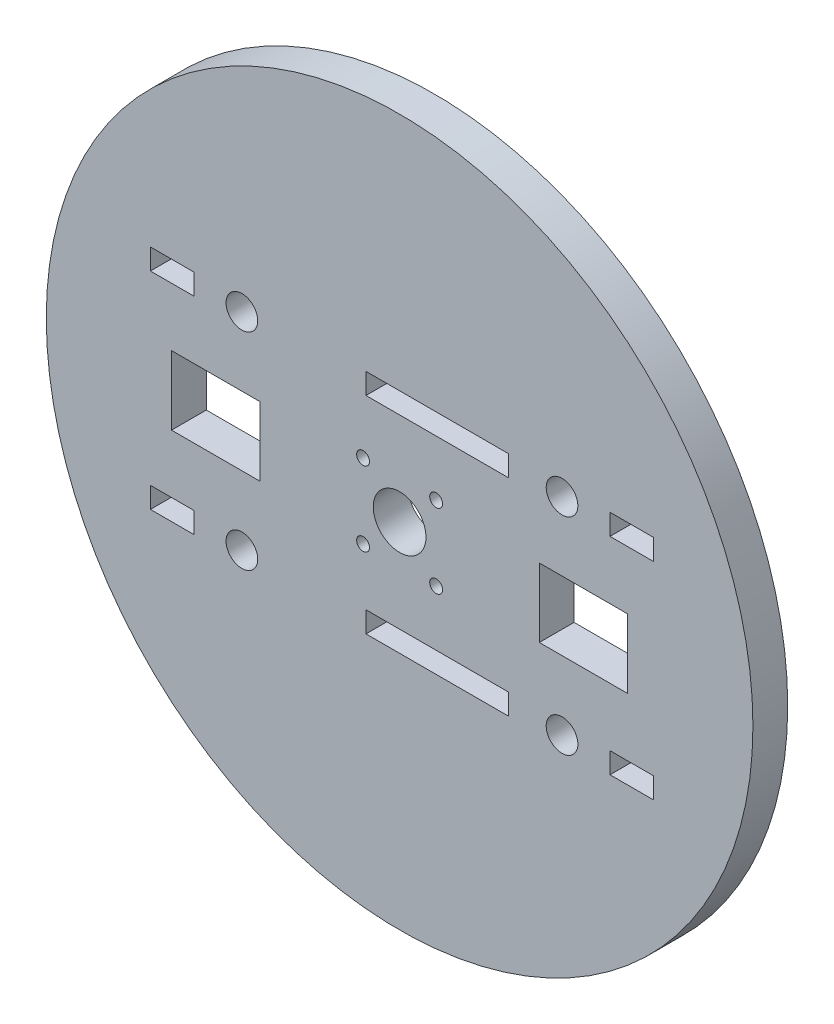
SolidWorks part; units mm, degrees
ref_plane "Front Plane" through (0, 0, 0) normal (0, 0, 1) x (1, 0, 0)
ref_plane "Top Plane" through (0, 0, 0) normal (0, 1, 0) x (1, 0, 0)
ref_plane "Right Plane" through (0, 0, 0) normal (1, 0, 0) x (0, 0, -1)
sketch "Sketch3" plane through (0, 0, 0) normal (0, 0, 1) x (1, 0, 0)
  line L4 (27.9395, 102.4605) -> (40.6396, 102.4605)
  line L5 (27.9395, 102.4605) -> (27.9395, 112.3605)
  line L6 (40.6396, 102.4605) -> (40.6396, 112.3605)
  line L7 (27.9395, 112.3605) -> (40.6396, 112.3605)
  line L8 (24.9039, 91.0784) -> (31.1539, 91.0784)
  line L9 (24.9039, 91.0784) -> (24.9039, 94.0784)
  line L10 (31.1539, 91.0784) -> (31.1539, 94.0784)
  line L11 (24.9039, 94.0784) -> (31.1539, 94.0784)
  line L12 (55.8789, 91.0784) -> (55.8789, 94.0784)
  line L13 (55.8789, 91.0784) -> (76.3789, 91.0784)
  line L14 (55.8789, 94.0784) -> (76.3789, 94.0784)
  line L15 (76.3789, 91.0784) -> (76.3789, 94.0784)
  line L24 (90.9439, 91.0784) -> (97.1939, 91.0784)
  line L25 (90.9439, 91.0784) -> (90.9439, 94.0784)
  line L26 (97.1939, 91.0784) -> (97.1939, 94.0784)
  line L27 (90.9439, 94.0784) -> (97.1939, 94.0784)
  line L28 (23.0523, 92.5784) -> (101.1168, 92.5784) construction
  line L29 (66.1289, 94.0784) -> (66.1289, 107.4105) construction
  line L30 (90.9439, 91.0784) -> (97.1939, 91.0784)
  line L31 (90.9439, 94.0784) -> (97.1939, 94.0784)
  line L32 (55.8789, 91.0784) -> (76.3789, 91.0784)
  line L33 (55.8789, 94.0784) -> (76.3789, 94.0784)
  line L34 (24.9039, 91.0784) -> (31.1539, 91.0784)
  line L35 (24.9039, 94.0784) -> (31.1539, 94.0784)
  line L36 (24.9039, 120.7426) -> (31.1539, 120.7426)
  line L37 (24.9039, 123.7426) -> (31.1539, 123.7426)
  line L38 (55.8789, 120.7426) -> (76.3789, 120.7426)
  line L39 (55.8789, 123.7426) -> (76.3789, 123.7426)
  line L40 (90.9439, 120.7426) -> (97.1939, 120.7426)
  line L41 (90.9439, 123.7426) -> (97.1939, 123.7426)
  line L42 (90.9439, 120.7426) -> (97.1939, 120.7426)
  line L43 (97.1939, 123.7426) -> (97.1939, 120.7426)
  line L44 (90.9439, 123.7426) -> (90.9439, 120.7426)
  line L45 (90.9439, 123.7426) -> (97.1939, 123.7426)
  line L46 (76.3789, 123.7426) -> (76.3789, 120.7426)
  line L47 (55.8789, 120.7426) -> (76.3789, 120.7426)
  line L48 (55.8789, 123.7426) -> (76.3789, 123.7426)
  line L49 (55.8789, 123.7426) -> (55.8789, 120.7426)
  line L50 (24.9039, 120.7426) -> (31.1539, 120.7426)
  line L51 (31.1539, 123.7426) -> (31.1539, 120.7426)
  line L52 (24.9039, 123.7426) -> (24.9039, 120.7426)
  line L53 (24.9039, 123.7426) -> (31.1539, 123.7426)
  line L54 (80.784, 102.4605) -> (80.784, 112.3605)
  line L55 (93.4841, 102.4605) -> (80.784, 102.4605)
  line L56 (93.4841, 102.4605) -> (93.4841, 112.3605)
  line L57 (93.4841, 112.3605) -> (80.784, 112.3605)
  line L162 (60.7118, 107.4105) -> (60.7118, 0) construction
  line L167 (60.7118, 107.4105) -> (9.9433, 107.4105)
  circle A0 centre (60.7118, 107.4105) radius 50.7685
  circle A1 centre (60.7118, 107.4105) radius 3.785
  circle A5 centre (65.9618, 102.0605) radius 0.925
  circle A7 centre (38.0489, 92.5784) radius 2.275
  circle A9 centre (84.0509, 92.5784) radius 2.275
  circle A17 centre (84.0509, 122.2426) radius 2.275
  circle A18 centre (38.0489, 122.2426) radius 2.275
  circle A24 centre (55.4618, 102.0605) radius 0.925
  circle A25 centre (65.9618, 112.7605) radius 0.925
  circle A26 centre (55.4618, 112.7605) radius 0.925
  point P4 (24.9039, 92.5784)
  point P6 (40.6396, 107.4105)
  point P9 (94.0689, 91.0784)
  point P10 (31.1539, 92.5784)
  point P17 (28.0289, 94.0784)
  point P18 (55.8789, 92.5784)
  point P19 (76.3789, 92.5784)
  point P21 (90.9439, 92.5784)
  point P22 (97.1939, 92.5784)
  point P23 (27.9395, 107.4105)
  dimension "D17" = 101.537
  dimension "D19" = 1.85
  dimension "D21" = 7.57
  dimension "D10" = 4.55
  dimension "D12" = 4.55
  dimension "D3" = 60.7118
  dimension "D4" = 14.8321
  dimension "D5" = 20.5
  dimension "D6" = 5.4171
  dimension "D7" = 27.94
  dimension "D8" = 6.25
  dimension "D9" = 3
  dimension "D11" = 28.08
  dimension "D13" = 38.1
  dimension "D14" = 6.25
  dimension "D15" = 0
  dimension "D16" = 17.922
  dimension "D18" = 107.4105
  dimension "D20" = 5.25
  dimension "D22" = 5.35
  dimension "D23" = 9.9
  dimension "D24" = 12.7001
  dimension "D25" = 20.0722
extrude "Boss-Extrude7" add sketch "Sketch3" along normal blind 5 separate body contours L167 L6 L7 L5 | L6 L167 L5 L4 | L37 L52 L36 L51 | L39 L49 L38 L46 | L41 L44 L40 L43 | L11 L9 L8 L10 | A7 | L13 L15 L14 L12 | A9 | L27 L25 L24 L26
